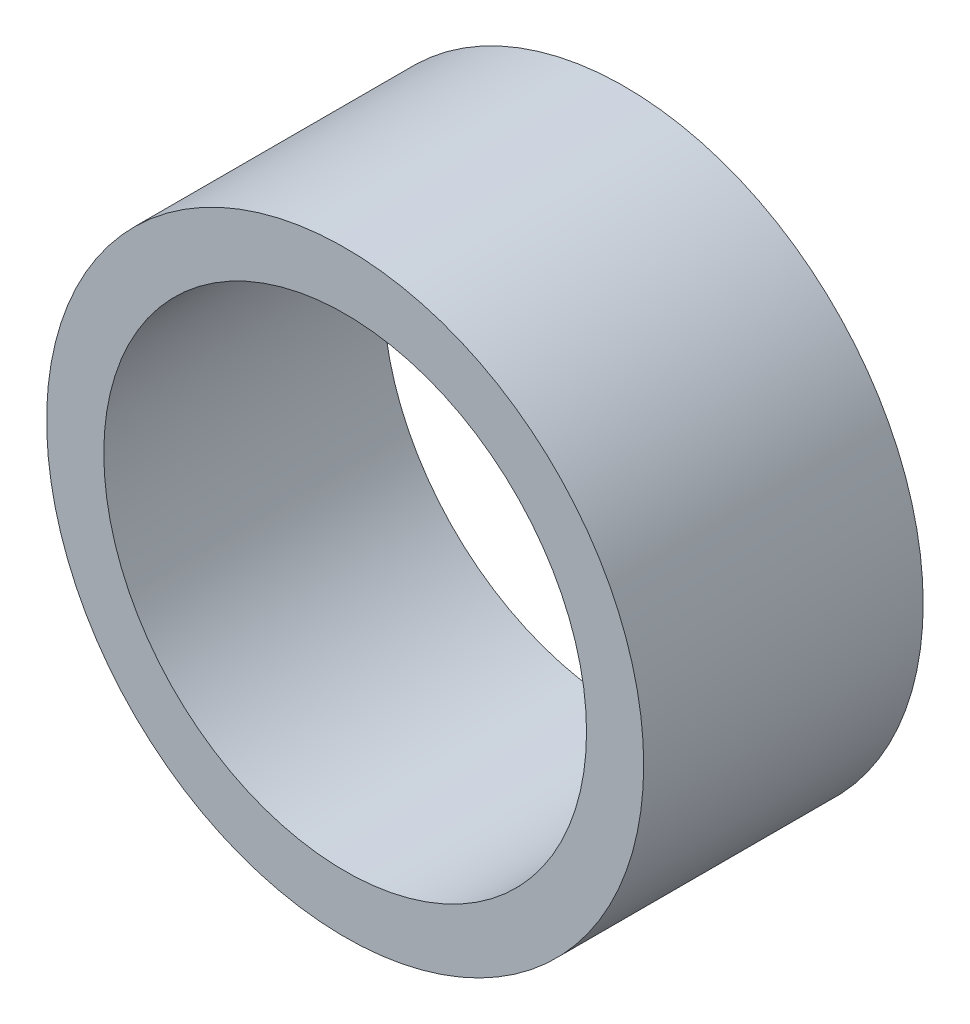
SolidWorks part; units mm, degrees
ref_plane "Plan de face" through (0, 0, 0) normal (0, 0, 1) x (1, 0, 0)
ref_plane "Plan de dessus" through (0, 0, 0) normal (0, 1, 0) x (1, 0, 0)
ref_plane "Plan de droite" through (0, 0, 0) normal (1, 0, 0) x (0, 0, -1)
sketch "Esquisse1" plane through (0, 0, 0) normal (0, 0, 1) x (1, 0, 0)
  circle A0 centre (0, 0) radius 19
  circle A1 centre (0, 0) radius 23.5
  dimension "D1" = 38
  dimension "D2" = 47
extrude "Boss.-Extru.1" add sketch "Esquisse1" along normal blind 22
